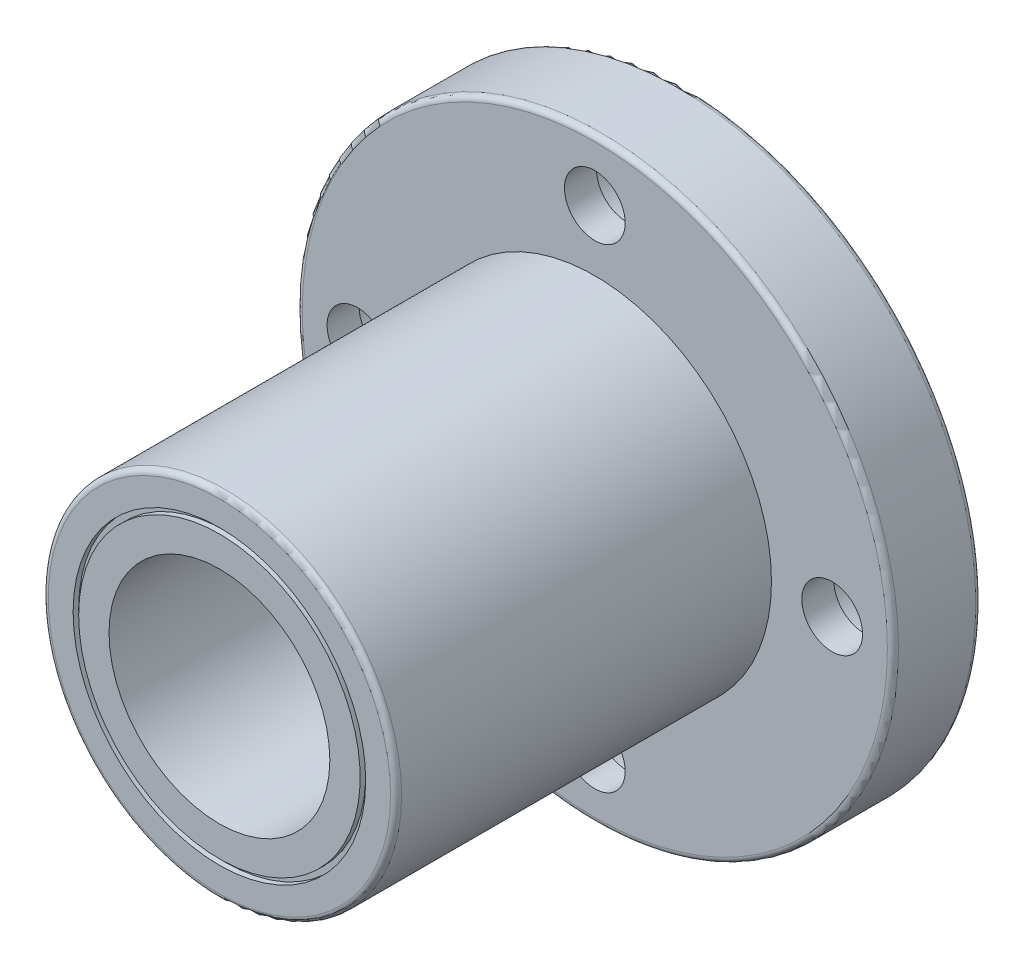
SolidWorks part; units mm, degrees
material "AISI 316 Отожженная нержавеющая сталь. полоса (SS)"
ref_plane "Plano frontal" through (0, 0, 0) normal (0, 0, 1) x (1, 0, 0)
ref_plane "Plano superior" through (0, 0, 0) normal (0, 1, 0) x (1, 0, 0)
ref_plane "Plano direito" through (0, 0, 0) normal (1, 0, 0) x (0, 0, -1)
sketch "Esboço1" plane through (0, 0, 0) normal (1, 0, 0) x (0, 0, -1)
  line L0 (0, 10) -> (0, 12.75)
  line L1 (0, 27) -> (-8, 27)
  line L2 (-8, 27) -> (-8, 16)
  line L3 (-8, 16) -> (-42, 16)
  line L4 (-42, 16) -> (-42, 13.25)
  line L5 (-42, 10) -> (0, 10)
  line L6 (0, 0) -> (-226.2321, 0) construction
  line L7 (-42, 13.25) -> (-41.5, 13.25)
  line L8 (-41.5, 13.25) -> (-41.5, 12.75)
  line L9 (-41.5, 12.75) -> (-42, 12.75)
  line L10 (0, 16) -> (-0.5, 16)
  line L11 (-0.5, 16) -> (-0.5, 15.5)
  line L12 (-0.5, 15.5) -> (0, 15.5)
  line L13 (0, 16) -> (0, 27)
  line L14 (-42, 12.75) -> (-42, 10)
  line L15 (0, 13.25) -> (-0.5, 13.25)
  line L16 (-0.5, 13.25) -> (-0.5, 12.75)
  line L17 (-0.5, 12.75) -> (0, 12.75)
  line L18 (0, 13.25) -> (0, 15.5)
  dimension "D1" = 42
  dimension "D2" = 32
  dimension "D3" = 20
  dimension "D4" = 54
  dimension "D5" = 8
  dimension "D6" = 0.5
  dimension "D7" = 0.5
  dimension "D8" = 0.5
  dimension "D9" = 0.5
  dimension "D10" = 0.5
  dimension "D11" = 0.5
revolve "Revolução1" add sketch "Esboço1" angle 360 about L6
sketch "Esboço5" plane through (0, 0, 0) normal (1, 0, 0) x (0, 0, -1)
  line L0 (0, 26) -> (-5.1, 26)
  line L1 (0, -27) -> (0, 27) construction
  line L2 (-5.1, 26) -> (-5.1, 24.25)
  line L3 (-5.1, 24.25) -> (-8, 24.25)
  line L4 (-8, 27) -> (-8, -27) construction
  line L5 (-8, 24.25) -> (-8, 21.5)
  line L6 (-8, 21.5) -> (0, 21.5)
  line L7 (0, 21.5) -> (0, 26)
  line L8 (0, 21.5) -> (2.2336, 21.5) construction
  line L9 (0, 0) -> (9.7959, 0) construction
  dimension "D1" = 9
  dimension "D2" = 5.5
  dimension "D3" = 5.1
  dimension "D4" = 43
revolve "Corte-Revolução1" cut sketch "Esboço5" angle 360 about L8
pattern_circular "PadrãoCircular1" count 4 over 360 about axis through (0, 0, 0) along (0, 0, 1) of "Corte-Revolução1"
fillet "Filete1" radius 0.5 3 edges at (-27, 0, 0) (-27, 0, 8) (-16, 0, 42)
